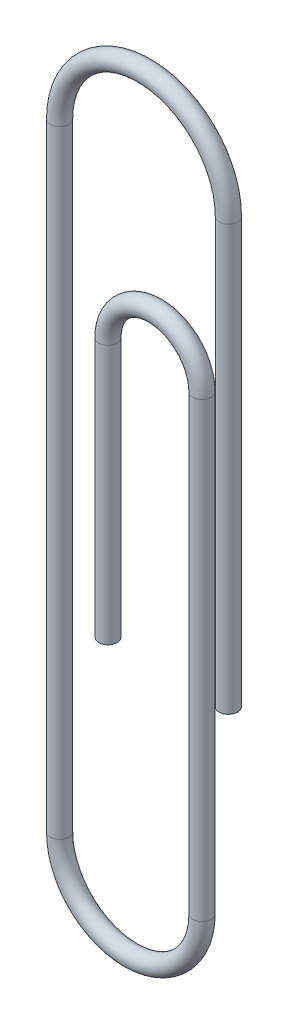
SolidWorks part; units mm, degrees
material "Plain Carbon Steel"
ref_plane "Front Plane" through (0, 0, 0) normal (0, 0, 1) x (1, 0, 0)
ref_plane "Top Plane" through (0, 0, 0) normal (0, 1, 0) x (1, 0, 0)
ref_plane "Right Plane" through (0, 0, 0) normal (1, 0, 0) x (0, 0, -1)
other "Center of Mass"
sketch "Sketch1" plane through (0, 0, 0) normal (0, 0, 1) x (1, 0, 0)
  line L0 (0, 0) -> (0, 17.38)
  line L1 (-6.91, 17.38) -> (-6.91, -7.89)
  line L2 (-1.08, -7.89) -> (-1.08, 10.62)
  line L3 (-4.93, 10.62) -> (-4.93, 0)
  arc A0 (0, 17.38) -> (-6.91, 17.38) centre (-3.455, 17.38) ccw
  arc A1 (-6.91, -7.89) -> (-1.08, -7.89) centre (-3.995, -7.89) ccw
  arc A2 (-1.08, 10.62) -> (-4.93, 10.62) centre (-3.005, 10.62) ccw
  point P12 (-3.455, 20.835)
  point P13 (-3.995, -10.805)
  dimension "D1" = 31.64
  dimension "D2" = 5.83
  dimension "D3" = 6.91
  dimension "D4" = 3.85
  dimension "D5" = 7.89
  dimension "D6" = 6.76
  dimension "D7" = 7.89
sweep "Sweep1" add path "Sketch1" circular profile diameter 0.76 parameters "D3"=0.76
